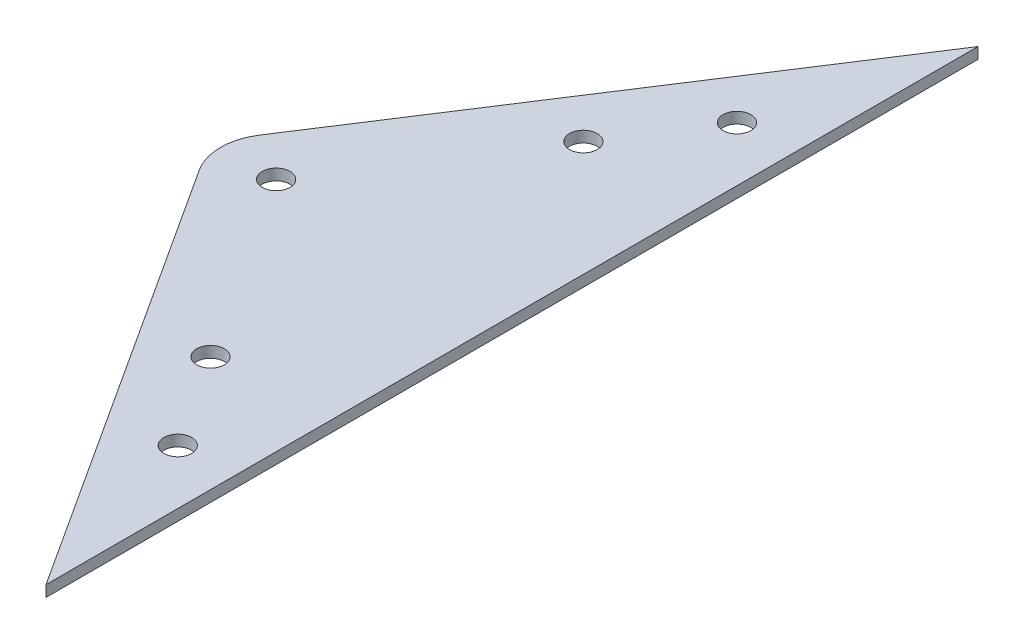
SolidWorks part; units mm, degrees
ref_plane "Front Plane" through (0, 0, 0) normal (0, 0, 1) x (1, 0, 0)
ref_plane "Top Plane" through (0, 0, 0) normal (0, 1, 0) x (1, 0, 0)
ref_plane "Right Plane" through (0, 0, 0) normal (1, 0, 0) x (0, 0, -1)
sketch "Sketch1" plane through (0, 0, 0) normal (0, 1, 0) x (1, 0, 0)
  line L0 (63.731, -373.2545) -> (114.5963, -294.779)
  line L1 (114.5963, -294.779) -> (114.5963, -462.6081)
  line L2 (114.5963, -462.6081) -> (63.731, -384.1326)
  circle A0 centre (72.1225, -378.6935) radius 2.5
  circle A1 centre (93.8787, -345.1277) radius 2.5
  circle A2 centre (104.7569, -328.3448) radius 2.5
  circle A3 centre (93.8787, -412.2594) radius 2.5
  circle A4 centre (104.7569, -429.0423) radius 2.5
  arc A5 (63.731, -373.2545) -> (63.731, -384.1326) centre (72.1225, -378.6935) ccw
  point P15 (60.2056, -378.6935)
  dimension "D4" = 5
  dimension "D5" = 5
  dimension "D6" = 5
  dimension "D7" = 5
  dimension "D8" = 5
  dimension "D19" = 10
  dimension "D1" = 114.1
  dimension "D2" = 100
  dimension "D3" = 100
  dimension "D9" = 10
  dimension "D10" = 10
  dimension "D11" = 10
  dimension "D12" = 10
  dimension "D13" = 10
  dimension "D14" = 10
  dimension "D15" = 40
  dimension "D16" = 20
  dimension "D17" = 40
  dimension "D18" = 20
extrude "Boss-Extrude1" add sketch "Sketch1" along normal blind 2
